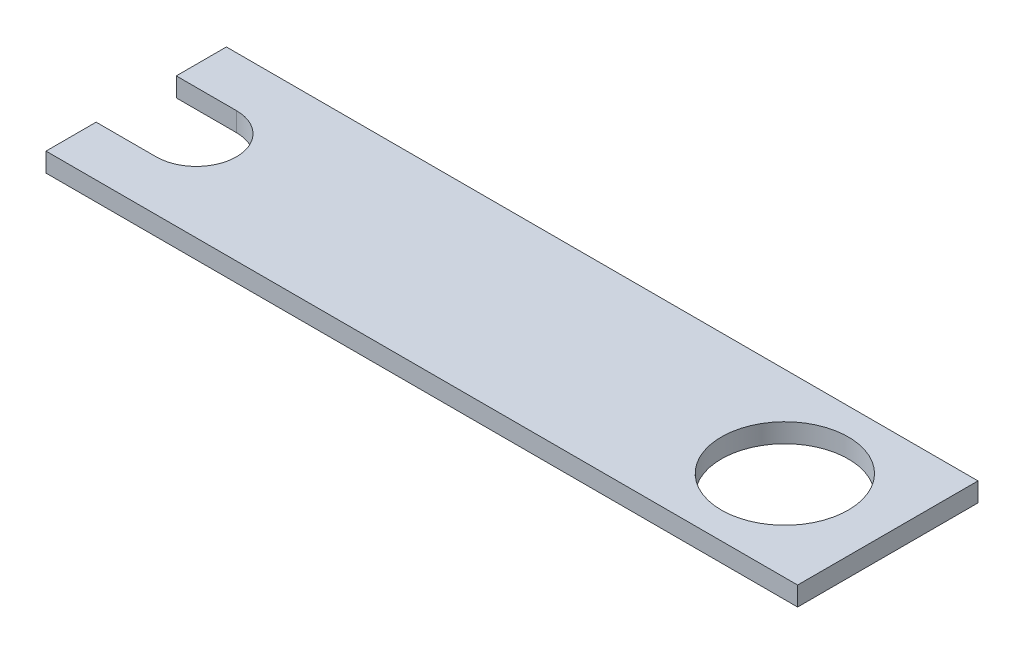
SolidWorks part; units mm, degrees
ref_plane "Front" through (0, 0, 0) normal (0, 0, 1) x (1, 0, 0)
ref_plane "Top" through (0, 0, 0) normal (0, 1, 0) x (1, 0, 0)
ref_plane "Right" through (0, 0, 0) normal (1, 0, 0) x (0, 0, -1)
sketch "Sketch1" plane through (0, 0, 0) normal (0, 1, 0) x (1, 0, 0)
  line L0 (-195.75, 13.33) -> (-215.75, 13.33)
  line L1 (34.25, 30) -> (-215.75, 30)
  line L2 (34.25, 30) -> (34.25, -30)
  line L3 (34.25, -30) -> (-215.75, -30)
  line L4 (-215.75, 13.33) -> (-215.75, 30)
  line L5 (-215.75, -13.33) -> (-195.75, -13.33)
  line L6 (-215.75, -13.33) -> (-215.75, -30)
  circle A0 centre (0, 0) radius 21.1
  arc A1 (-195.75, -13.33) -> (-195.75, 13.33) centre (-195.75, 0) ccw
  point P0 (0, 0)
  dimension "D1" = 42.2
  dimension "D2" = 250
  dimension "D3" = 26.66
  dimension "D8" = 161.32
  dimension "D4" = 60
  dimension "D5" = 30
  dimension "D7" = 30
extrude "Boss-Extrude1" add sketch "Sketch1" along normal blind 6.35
